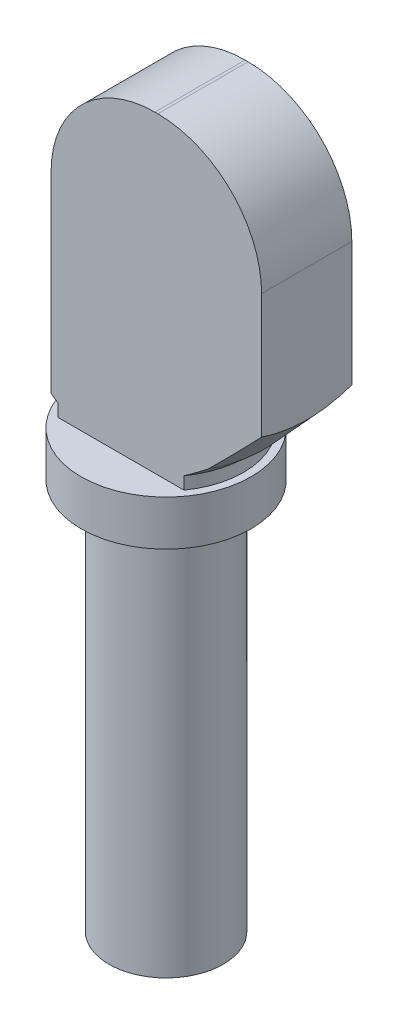
SolidWorks part; units mm, degrees
ref_plane "Front" through (0, 0, 0) normal (0, 0, 1) x (1, 0, 0)
ref_plane "Top" through (0, 0, 0) normal (0, 1, 0) x (1, 0, 0)
ref_plane "Right" through (0, 0, 0) normal (1, 0, 0) x (0, 0, -1)
sketch "Sketch1" plane through (0, 0, 0) normal (0, 0, 1) x (1, 0, 0)
  line L0 (0, 0) -> (0, 22.0717) construction
  line L1 (0, 0) -> (1.9, 0)
  line L2 (1.9, 0) -> (1.9, 13)
  line L3 (1.9, 13) -> (2.825, 13)
  line L4 (2.825, 13) -> (2.825, 14.5)
  line L5 (2.825, 14.5) -> (0, 14.5)
  line L6 (0, 14.5) -> (0, 0)
  dimension "D1" = 3.8
  dimension "D2" = 13
  dimension "D3" = 5.65
  dimension "D4" = 1.5
revolve "Revolve1" add sketch "Sketch1" angle 360 about L0
sketch "Sketch2" plane through (0, 0, 0) normal (0, 0, 1) x (1, 0, 0)
  line L0 (-2.325, 14.5) -> (-2.325, 21.45)
  line L1 (2.825, 14.5) -> (-2.825, 14.5) construction
  line L2 (1.125, 24.9) -> (1.225, 24.9)
  line L3 (4.675, 21.45) -> (4.675, 15.5)
  line L4 (4.675, 15.5) -> (2.575, 15)
  line L5 (2.575, 15) -> (2.575, 14.5)
  line L6 (2.575, 14.5) -> (-2.325, 14.5)
  line L7 (-2.825, 14.5) -> (-2.825, 13) construction
  arc A0 (1.225, 24.9) -> (4.675, 21.45) centre (1.225, 21.45) cw
  arc A1 (-2.325, 21.45) -> (1.125, 24.9) centre (1.125, 21.45) cw
  dimension "D6" = 3.45
  dimension "D7" = 3.45
  dimension "D1" = 0.5
  dimension "D2" = 4.9
  dimension "D3" = 0.5
  dimension "D4" = 7
  dimension "D5" = 10.4
  dimension "D8" = 1
extrude "Boss-Extrude1" add sketch "Sketch2" along normal mid plane 3
sketch "Sketch3" plane through (0, 0, 0) normal (0, 0, 1) x (1, 0, 0)
  line L0 (3.25, 15.5) -> (5.35, 17.8) construction
  line L1 (3.25, 15.5) -> (5.35, 17.8)
  line L2 (3.25, 15.5) -> (2.575, 14.913)
  line L5 (2.575, 14.5) -> (6.2888, 14.5)
  line L6 (6.2888, 14.5) -> (6.2888, 17.8)
  line L7 (6.2888, 17.8) -> (5.35, 17.8)
  line L8 (0, 0) -> (0, 26.5487) construction
  line L9 (2.575, 14.913) -> (2.575, 14.5)
  line L10 (2.575, 14.5) -> (2.575, 15) construction
revolve "DELETE CUT TO SEE REAL COMPONENT" cut sketch "Sketch3" angle 360 about L8
